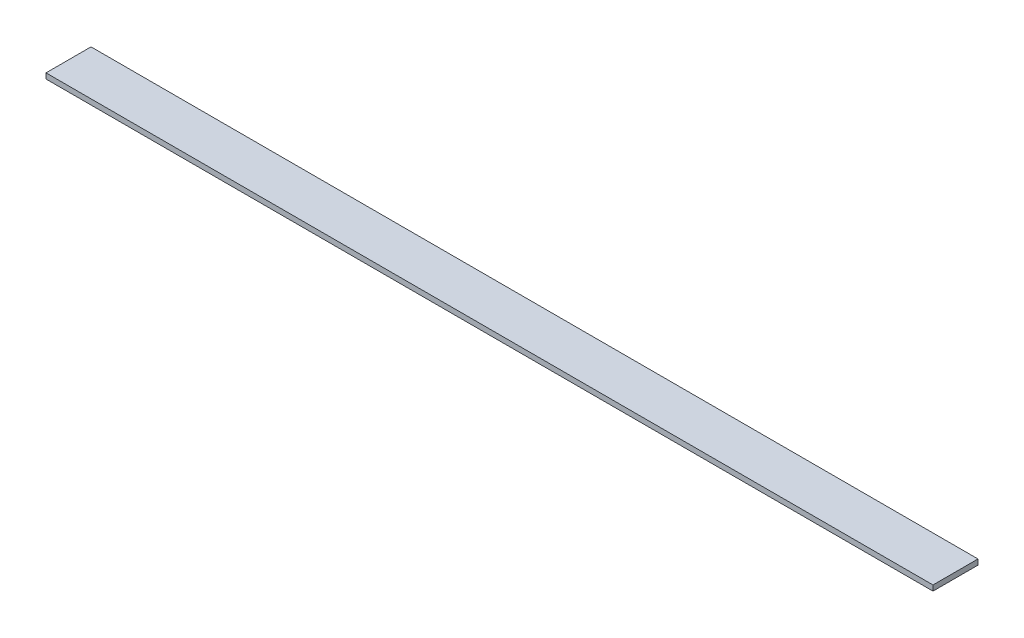
SolidWorks part; units mm, degrees
ref_plane "Front Plane" through (0, 0, 0) normal (0, 0, 1) x (1, 0, 0)
ref_plane "Top Plane" through (0, 0, 0) normal (0, 1, 0) x (1, 0, 0)
ref_plane "Right Plane" through (0, 0, 0) normal (1, 0, 0) x (0, 0, -1)
sketch "Sketch1" plane through (0, 0, 0) normal (1, 0, 0) x (0, 0, -1)
  line L1 (8.375, -1) -> (-8.375, -1)
  line L2 (8.375, -1) -> (8.375, 1)
  line L3 (8.375, 1) -> (-8.375, 1)
  line L4 (-8.375, -1) -> (-8.375, 1)
  line L5 (8.375, -1) -> (-8.375, 1) construction
  line L6 (8.375, 1) -> (-8.375, -1) construction
  point P0 (0, 0)
  dimension "D1" = 16.75
  dimension "D2" = 2
extrude "Boss-Extrude1" add sketch "Sketch1" along normal mid plane 330
